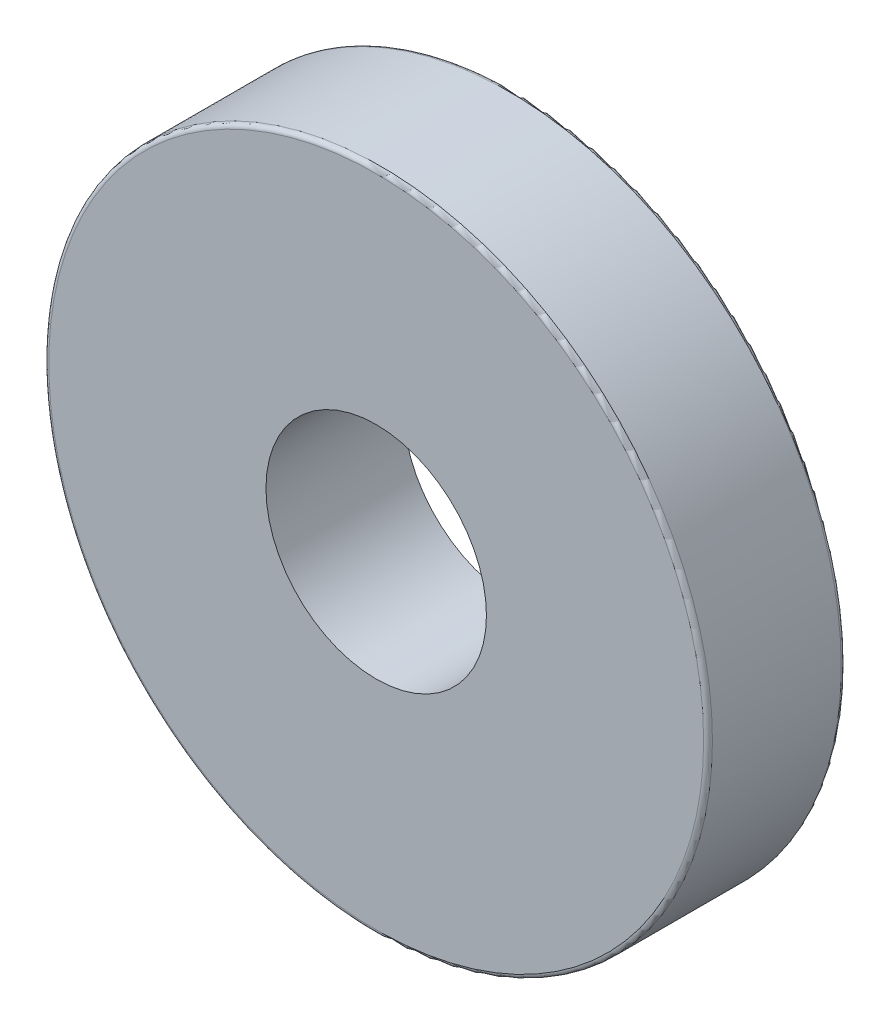
SolidWorks part; units mm, degrees
ref_plane "Front Plane" through (0, 0, 0) normal (0, 0, 1) x (1, 0, 0)
ref_plane "Top Plane" through (0, 0, 0) normal (0, 1, 0) x (1, 0, 0)
ref_plane "Right Plane" through (0, 0, 0) normal (1, 0, 0) x (0, 0, -1)
sketch "Sketch1" plane through (0, 0, 0) normal (0, 1, 0) x (1, 0, 0)
  line L0 (1.143, 0) -> (10.5251, 0)
  line L1 (10.7156, 0.1905) -> (10.7156, 5.7531)
  line L2 (10.5251, 5.9436) -> (1.143, 5.9436)
  line L3 (1.143, 5.9436) -> (1.143, 0)
  line L4 (-3.6195, 5.9436) -> (-3.6195, 0) construction
  arc A0 (10.5251, 0) -> (10.7156, 0.1905) centre (10.5251, 0.1905) ccw
  arc A1 (10.7156, 5.7531) -> (10.5251, 5.9436) centre (10.5251, 5.7531) ccw
  dimension "D1" = 4.7625
  dimension "D2" = 9.3821
revolve "Revolve1" add sketch "Sketch1" angle 360 about L4
